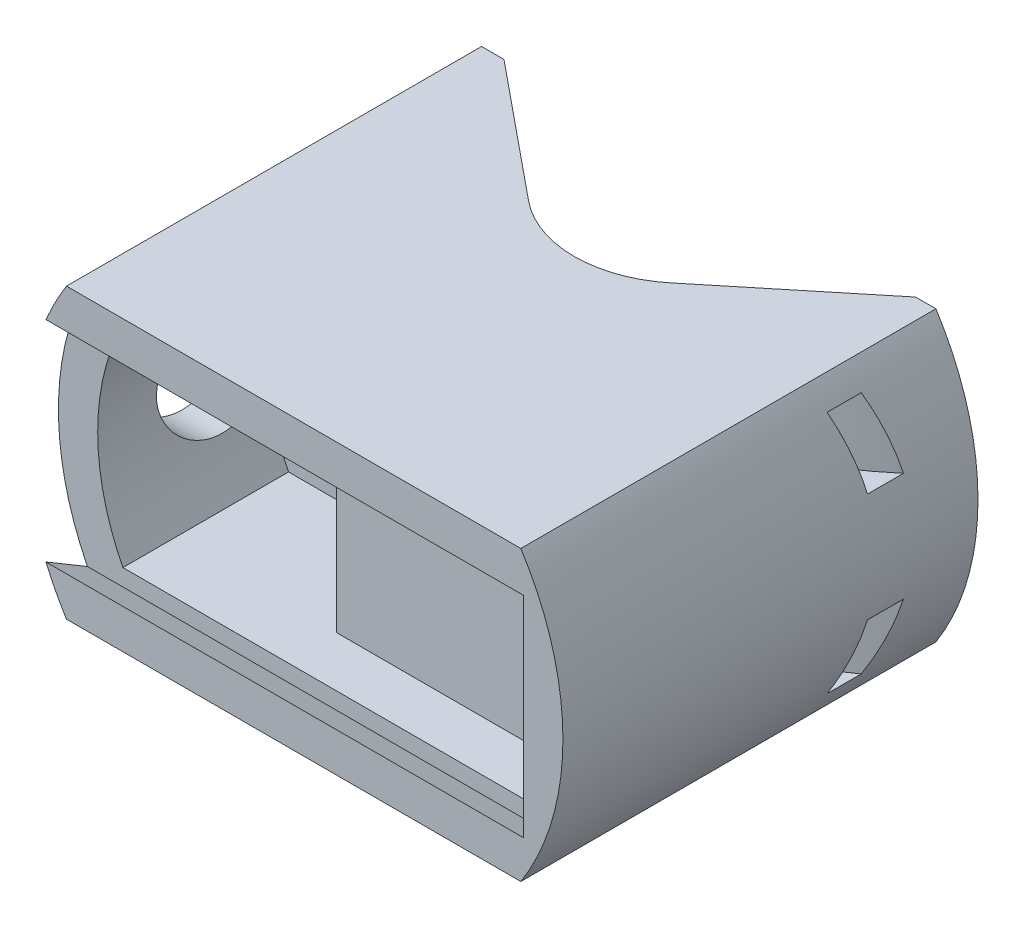
SolidWorks part; units mm, degrees
ref_plane "Front Plane" through (0, 0, 0) normal (0, 0, 1) x (1, 0, 0)
ref_plane "Top Plane" through (0, 0, 0) normal (0, 1, 0) x (1, 0, 0)
ref_plane "Right Plane" through (0, 0, 0) normal (1, 0, 0) x (0, 0, -1)
sketch "Sketch2" plane through (0, 0, 0) normal (0, 0, 1) x (1, 0, 0)
  line L0 (17.8318, 8.8565) -> (17.8318, -8.8565) construction
  line L1 (-18.0035, 8.8565) -> (-18.0035, -8.8565) construction
  line L2 (-18.0035, 8.8565) -> (17.8318, -8.8565) construction
  line L3 (17.8318, 8.8565) -> (-18.0035, -8.8565) construction
  line L4 (17.8318, 8.8565) -> (-18.0035, 8.8565)
  line L5 (-18.0035, -8.8565) -> (17.8318, -8.8565)
  arc A4 (17.8318, -8.8565) -> (17.8318, 8.8565) centre (0, 0) ccw
  arc A5 (-18.0035, 8.8565) -> (-18.0035, -8.8565) centre (0.0362, 0) ccw
  point P0 (-26.822, -24.1998)
  dimension "D3" = 19.9101
  dimension "D4" = 20.0964
  dimension "D1" = 35.8353
  dimension "D2" = 17.713
sketch "Sketch3" plane through (0, 0, 0) normal (0, 1, 0) x (1, 0, 0)
  line L8 (-18.7534, 0) -> (-19.9546, 0)
  line L9 (-18.7534, 10.7645) -> (-18.7534, 0)
  line L10 (-4.7881, 10.7645) -> (-18.7534, 10.7645)
  line L11 (-4.7881, 0) -> (-4.7881, 10.7645)
  line L12 (19.9546, 0) -> (-4.7881, 0)
  line L13 (19.9546, -1.672) -> (19.9546, 0)
  line L14 (-19.9546, -1.672) -> (19.9546, -1.672)
  line L15 (-19.9546, 0) -> (-19.9546, -1.672)
  line L16 (0, -1.672) -> (0, 0) construction
  point P11 (0, 0)
  point P12 (0, 0)
  point P13 (-19.9546, -3.7196)
  point P14 (-19.999, -3.0094)
  point P15 (0, 0)
  point P16 (0, 0)
  point P17 (0, 0)
  dimension "D1" = 10.7645
  dimension "D2" = 13.9653
  dimension "D3" = 1.672
  dimension "D4" = 39.9091
  dimension "D5" = 1.2012
sketch "Sketch5" plane through (0, 0, 0) normal (1, 0, 0) x (0, 0, -1)
  line L5 (6.385, 4.7124) -> (-0.015, 4.7124)
  line L6 (6.385, -4.2876) -> (10.685, -4.2876)
  line L7 (6.385, -4.2876) -> (-0.015, -4.2876)
  line L8 (10.785, -4.1876) -> (10.785, 4.6124)
  line L9 (10.685, 4.7124) -> (6.385, 4.7124)
  line L10 (0, 0) -> (10.785, 0) construction
  arc A1 (6.485, -3.9876) -> (6.485, 4.4124) centre (6.485, 0.2124) ccw
  arc A2 (6.485, 4.4124) -> (6.485, -3.9876) centre (6.5838, 0.2124) cw
  point P15 (0, 0)
  dimension "D1" = 8.8
sketch "Sketch7" plane through (0, 0, 0) normal (0, 0, 1) x (1, 0, 0)
  line L4 (-20.3439, -12.8565) -> (20.1594, -12.8565)
  line L5 (20.1594, 12.8565) -> (-20.3439, 12.8565)
  line L6 (-20.3439, -12.8565) -> (20.1594, -12.8565)
  line L7 (20.1594, 12.8565) -> (-20.3439, 12.8565)
  arc A4 (20.1594, -12.8565) -> (20.1594, 12.8565) centre (0, 0) ccw
  arc A5 (-20.3439, 12.8565) -> (-20.3439, -12.8565) centre (0.0362, 0) ccw
  arc A6 (20.1594, -12.8565) -> (20.1594, 12.8565) centre (0, 0) ccw
  arc A7 (-20.3439, 12.8565) -> (-20.3439, -12.8565) centre (0.0362, 0) ccw
  dimension "D1" = 4
extrude "Boss-Extrude2" add sketch "Sketch7" against normal blind 30 and the other way blind 7
sketch "Sketch8" plane through (0, 12.8565, 0) normal (0, 1, 0) x (1, 0, 0)
  line L0 (-18.3439, 30) -> (0, 30)
  line L1 (20.1594, 30) -> (-20.3439, 30) construction
  line L2 (0, 30) -> (0, 15)
  line L3 (0, 15) -> (-18.3439, 30)
  line L4 (0, 0) -> (0, 46.7563) construction
  point P9 (-0.0922, 30)
  point P10 (0, 0)
  point P11 (0, 30)
  dimension "D1" = 15
  dimension "D2" = 2
extrude "Cut-Extrude1" cut sketch "Sketch8" against normal up to surface (25.713 mm away) up to face at (-0.0922, -12.8565, -11.5)
mirror "Mirror1" about plane through (0, 0, 0) normal (1, 0, 0) of "Cut-Extrude1"
fillet "Fillet1" radius 10 1 edges at (0, 0, -15)
ref_plane "Plane3" through (0, 0, 0) normal (0, 1, 0) x (1, 0, 0)
ref_plane "Plane4" through (0, 0, -10.7645) normal (0, 0, -1) x (-1, 0, 0)
sketch "Sketch9" plane through (0, 0, 7) normal (0, 0, 1) x (1, 0, 0)
  line L4 (-18.3123, -9.3565) -> (18.1391, -9.3565)
  line L5 (18.1391, 9.3565) -> (-18.3123, 9.3565)
  line L6 (-18.3123, -9.3565) -> (18.1391, -9.3565)
  line L7 (18.1391, 9.3565) -> (-18.3123, 9.3565)
  arc A4 (18.1391, -9.3565) -> (18.1391, 9.3565) centre (0, 0) ccw
  arc A5 (-18.3123, 9.3565) -> (-18.3123, -9.3565) centre (0.0362, 0) ccw
  arc A6 (18.1391, -9.3565) -> (18.1391, 9.3565) centre (0, 0) ccw
  arc A7 (-18.3123, 9.3565) -> (-18.3123, -9.3565) centre (0.0362, 0) ccw
  dimension "D1" = 0.5
extrude "Cut-Extrude2" cut sketch "Sketch9" against normal up to surface (17.7645 mm away)
sketch "Sketch10" plane through (0, 0, -10.7645) normal (0, 0, -1) x (-1, 0, 0)
  line L3 (-17.8318, 8.8565) -> (18.0035, 8.8565) construction
  line L5 (3.2881, 8.8565) -> (3.2881, -8.8565)
  line L6 (18.0035, -8.8565) -> (-17.8318, -8.8565) construction
  line L10 (-17.8318, 8.8565) -> (3.2881, 8.8565)
  line L11 (3.2881, -8.8565) -> (-17.8318, -8.8565)
  line L12 (4.7881, 0) -> (4.7881, 8.8565) construction
  arc A2 (-17.8318, 8.8565) -> (-17.8318, -8.8565) centre (0, 0) ccw construction
  arc A3 (-17.8318, 8.8565) -> (-17.8318, -8.8565) centre (0, 0) ccw
  point P1 (0, 0)
  point P2 (11.7707, 0)
  dimension "D1" = 1.5
extrude "Boss-Extrude3" add sketch "Sketch10" against normal up to vertex (10.7645 mm away) up to point (-4.7881, 0, 0)
ref_plane "Plane5" through (-24.0602, 0, 0) normal (-1, 0, 0) x (0, 0, 1)
sketch "Sketch11" plane through (-24.0602, 0, 0) normal (-1, 0, 0) x (0, 0, 1)
  circle A0 centre (-6.485, 0.2124) radius 5.25
  dimension "D1" = 10.5
extrude "Cut-Extrude3" cut sketch "Sketch11" against normal up to surface (20.7721 mm away) up to face at (-3.2881, 0, -5.3823)
sketch "Sketch13" plane through (0, -12.8565, 0) normal (0, -1, 0) x (1, 0, 0)
  line L0 (0, -51.5676) -> (0, 0) construction
  circle A1 centre (0, -51.5676) radius 39.0208
  point P0 (0, -51.5676)
ref_axis "Axis1" through (0, -85.888, -51.5676) along (0, 1, 0)
sketch "Sketch12" plane through (0, 0, 0) normal (1, 0, 0) x (0, 0, -1)
  line L0 (-7, 12.8565) -> (30, 12.8565) construction
  line L1 (12.785, 10.8565) -> (15.285, 10.8565)
  line L2 (12.785, 10.8565) -> (12.785, 4.8565)
  line L3 (12.785, 4.8565) -> (15.285, 4.8565)
  line L4 (15.285, 10.8565) -> (15.285, 4.8565)
  line L5 (10.785, -4.1876) -> (10.785, 4.6124) construction
  line L6 (6.8514, 0) -> (-6.8514, 0) construction
  line L7 (12.785, -4.8565) -> (15.285, -4.8565)
  line L8 (15.285, -10.8565) -> (15.285, -4.8565)
  line L9 (12.785, -10.8565) -> (12.785, -4.8565)
  line L10 (12.785, -10.8565) -> (15.285, -10.8565)
  dimension "D1" = 6
  dimension "D2" = 2.5
  dimension "D3" = 2
  dimension "D4" = 2
revolve "Cut-Revolve1" cut sketch "Sketch12" angle 360 about axis through (0, -85.888, -51.5676) along (0, 1, 0)
sketch "Sketch14" plane through (-24.0602, 0, 0) normal (-1, 0, 0) x (0, 0, 1)
  line L0 (7, 9.3565) -> (4, 10.8565)
  line L2 (7, -12.8565) -> (7, 12.8565) construction
  line L18 (7, 12.8565) -> (-30, 12.8565) construction
  line L19 (4, 10.8565) -> (4, -10.8565)
  line L21 (7, -9.3565) -> (7, 9.3565)
  line L22 (6.8514, 0) -> (-6.8514, 0) construction
  line L23 (7, -9.3565) -> (4, -10.8565)
  point P4 (4, 8.8555)
  point P8 (0, 0)
  point P9 (0, 0)
  point P10 (0, 0)
  point P11 (4, 8.9737)
  point P12 (0, 0)
  dimension "D1" = 2
  dimension "D2" = 3.5
  dimension "D3" = 3
extrude "Cut-Extrude10" cut sketch "Sketch14" against normal up to vertex (6.7771 mm away)
